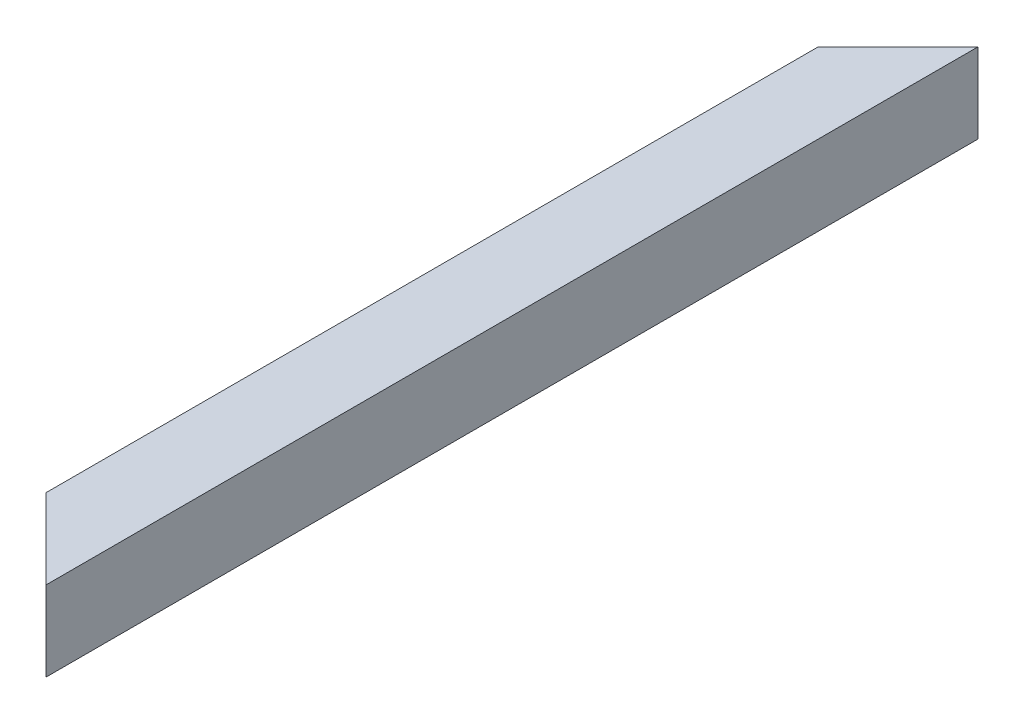
SolidWorks part; units mm, degrees
ref_plane "Front Plane" through (0, 0, 0) normal (0, 0, 1) x (1, 0, 0)
ref_plane "Top Plane" through (0, 0, 0) normal (0, 1, 0) x (1, 0, 0)
ref_plane "Right Plane" through (0, 0, 0) normal (1, 0, 0) x (0, 0, -1)
curve "Curve1"
  spline degree 1 poles (0, 0, 0) (0, 0, 700) knots 0 0 1 1
sketch "Sketch1" plane through (0, 0, 0) normal (0, 0, 1) x (1, 0, 0)
  line L0 (0, 35.3535) -> (0, -33.8384) construction
  line L1 (-30, 30) -> (30, 30)
  line L2 (-30, 30) -> (-30, -30)
  line L3 (-30, -30) -> (30, -30)
  line L4 (30, 30) -> (30, -30)
  line L5 (-26, 26) -> (26, 26)
  line L6 (-26, 26) -> (-26, -26)
  line L7 (-26, -26) -> (26, -26)
  line L8 (26, 26) -> (26, -26)
  line L9 (-39.3939, 0) -> (41.5152, 0) construction
  dimension "D1" = 60
  dimension "D2" = 52
sweep "Sweep1" add profiles "Sketch1" path "Curve1"
sketch "Sketch2" plane through (0, 30, 0) normal (0, 1, 0) x (1, 0, 0)
  line L0 (30, 0) -> (-30, -60)
  line L1 (-30, 0) -> (-30, -700) construction
  line L2 (-30, -60) -> (-30, 0)
  line L3 (-30, 0) -> (30, 0)
  line L4 (30, -700) -> (-30, -640)
  line L5 (-30, -640) -> (-30, -700)
  line L6 (-30, -700) -> (30, -700)
  dimension "D1" = 45
  dimension "D2" = 45
extrude "Cut-Extrude1" cut sketch "Sketch2" against normal through all
